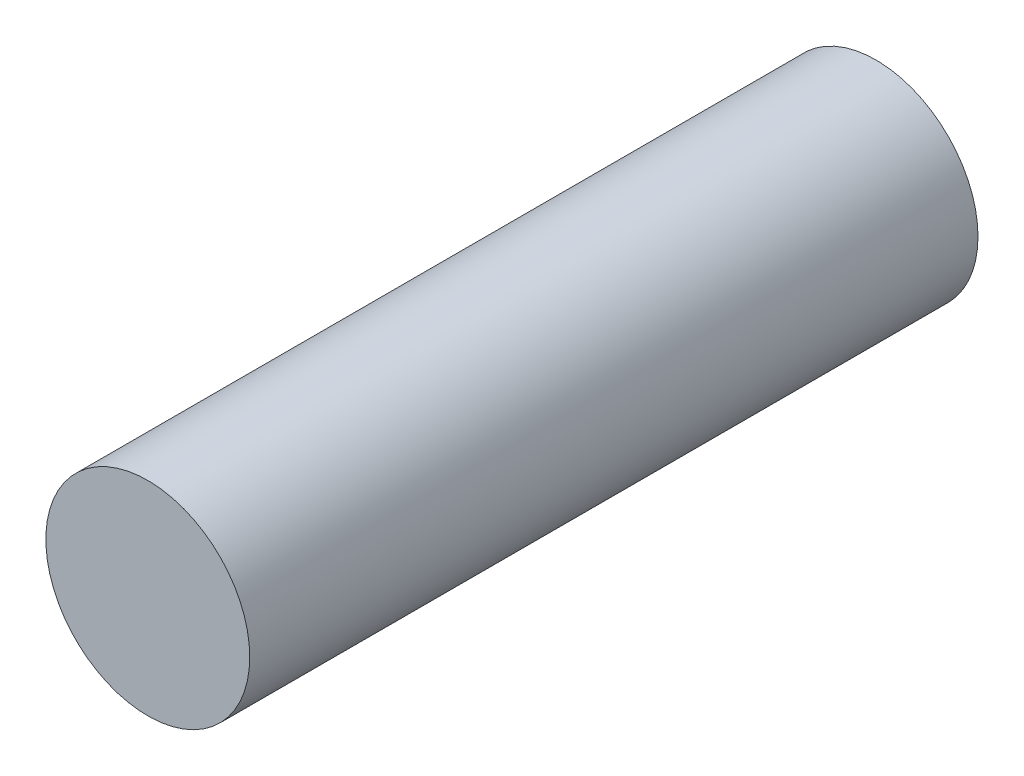
SolidWorks part; units mm, degrees
ref_plane "Front Plane" through (0, 0, 0) normal (0, 0, 1) x (1, 0, 0)
ref_plane "Top Plane" through (0, 0, 0) normal (0, 1, 0) x (1, 0, 0)
ref_plane "Right Plane" through (0, 0, 0) normal (1, 0, 0) x (0, 0, -1)
sketch "Sketch1" plane through (0, 0, 0) normal (0, 0, 1) x (1, 0, 0)
  circle A0 centre (0, 0) radius 3.5
  dimension "D1" = 7
extrude "Boss-Extrude1" add sketch "Sketch1" along normal blind 25
